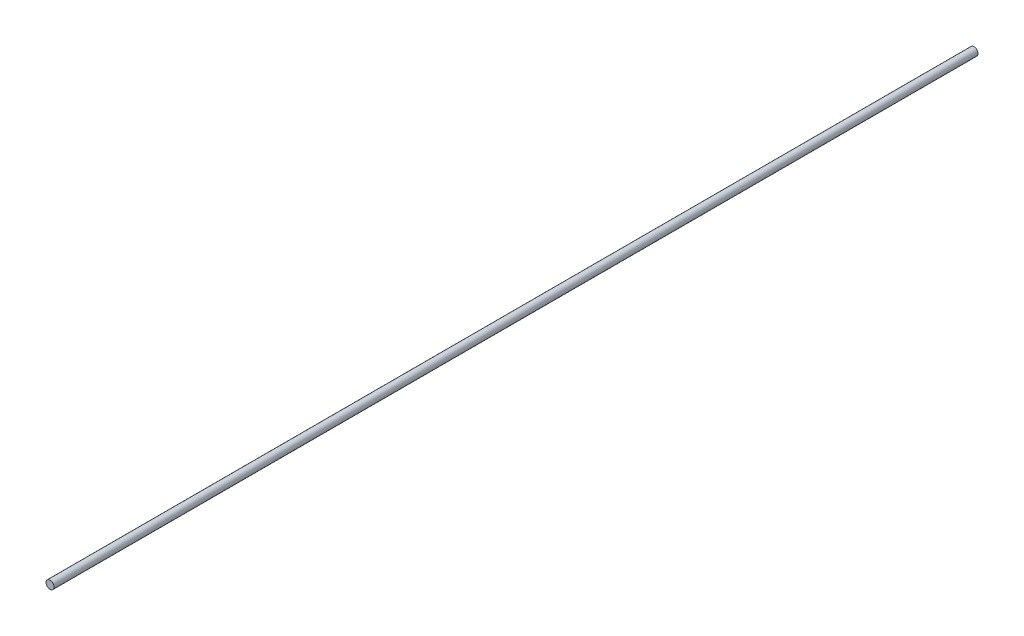
SolidWorks part; units mm, degrees
ref_plane "Front Plane" through (0, 0, 0) normal (0, 0, 1) x (1, 0, 0)
ref_plane "Top Plane" through (0, 0, 0) normal (0, 1, 0) x (1, 0, 0)
ref_plane "Right Plane" through (0, 0, 0) normal (1, 0, 0) x (0, 0, -1)
sketch "Sketch1" plane through (0, 0, 0) normal (0, 0, 1) x (1, 0, 0)
  circle A0 centre (0, 0) radius 7.9375
  dimension "D1" = 15.875
extrude "Boss-Extrude1" add sketch "Sketch1" along normal mid plane 1828.8
